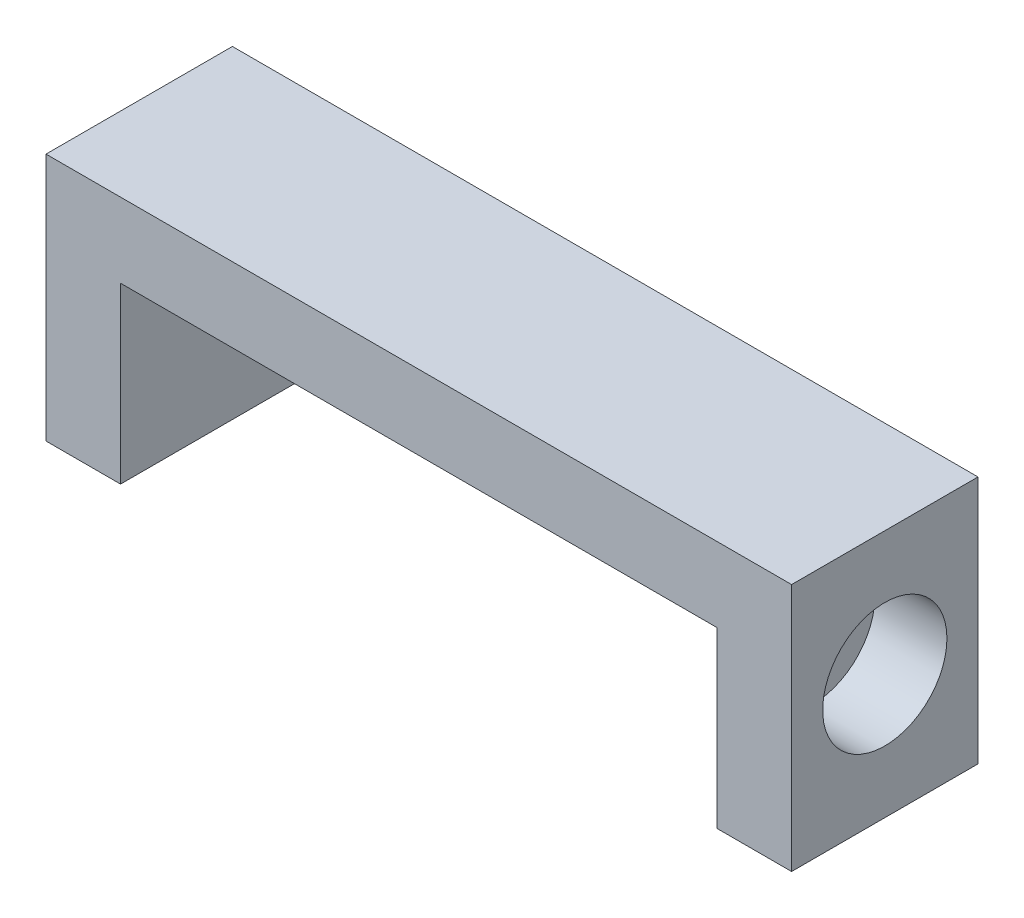
SolidWorks part; units mm, degrees
ref_plane "Front Plane" through (0, 0, 0) normal (0, 0, 1) x (1, 0, 0)
ref_plane "Top Plane" through (0, 0, 0) normal (0, 1, 0) x (1, 0, 0)
ref_plane "Right Plane" through (0, 0, 0) normal (1, 0, 0) x (0, 0, -1)
sketch "Sketch1" plane through (0, 0, 0) normal (0, 0, 1) x (1, 0, 0)
  line L0 (-15, -5) -> (-2.5, -5)
  line L1 (-15, -5) -> (15, -5)
  line L2 (-15, -5) -> (-15, 5)
  line L3 (-15, 5) -> (15, 5)
  line L4 (15, -5) -> (15, 5)
  line L5 (-15, -5) -> (15, 5) construction
  line L6 (-15, 5) -> (15, -5) construction
  line L7 (15, -5) -> (13.5, -5)
  line L8 (15, -5) -> (13.5, -5)
  point P0 (0, 0)
  dimension "D1" = 30
  dimension "D2" = 10
extrude "Boss-Extrude1" add sketch "Sketch1" along normal mid plane 7.5 contours L2 L1 L4 L3
sketch "Sketch2" plane through (0, 0, 3.75) normal (0, 0, 1) x (1, 0, 0)
  line L0 (-15, -5) -> (15, -5) construction
  line L1 (-12, -5) -> (12, -5)
  line L2 (-12, -5) -> (-12, 2)
  line L3 (-12, 2) -> (12, 2)
  line L4 (12, -5) -> (12, 2)
  line L5 (-15, -5) -> (-15, 5) construction
  line L6 (15, -5) -> (15, 5) construction
  line L7 (-15, 5) -> (15, 5) construction
  dimension "D1" = 3
  dimension "D2" = 3
  dimension "D3" = 3
extrude "Cut-Extrude1" cut sketch "Sketch2" against normal up to next
sketch "Sketch4" plane through (0, 0, 0) normal (1, 0, 0) x (0, 0, -1)
  circle A0 centre (0, 0) radius 2.5
  point P11 (0, 0)
  dimension "D1" = 5
extrude "Cut-Extrude2" cut sketch "Sketch4" against normal through all both and the other way through all
sketch "Sketch5" plane through (15, 0, 0) normal (1, 0, 0) x (0, 0, -1)
  circle A0 centre (0, 0) radius 2.5
  dimension "D1" = 5
extrude "Boss-Extrude2" add sketch "Sketch5" along normal blind 0.1 from surface at -3 starting at face at (12, -1.0833, 0)
sketch "Sketch6" plane through (-15, 0, 0) normal (-1, 0, 0) x (0, 0, 1)
  circle A0 centre (0, 0) radius 2.5
extrude "Boss-Extrude3" add sketch "Sketch6" along normal blind 0.1 from surface at -3 starting at face at (-12, -1.0833, 0)
sketch "Sketch7" plane through (0, 0, -3.75) normal (0, 0, -1) x (-1, 0, 0)
  line L0 (15, 5) -> (-15, 5) construction
  line L1 (-12, 2) -> (12, 2)
  line L2 (-12, 2) -> (-12, 5)
  line L3 (-12, 5) -> (12, 5)
  line L4 (12, 2) -> (12, 5)
  point P7 (0, 0)
  point P8 (12, 2)
extrude "Boss-Extrude4" add sketch "Sketch7" against normal up to surface (7.5 mm away) up to face at (0, -0.75, 3.75)
